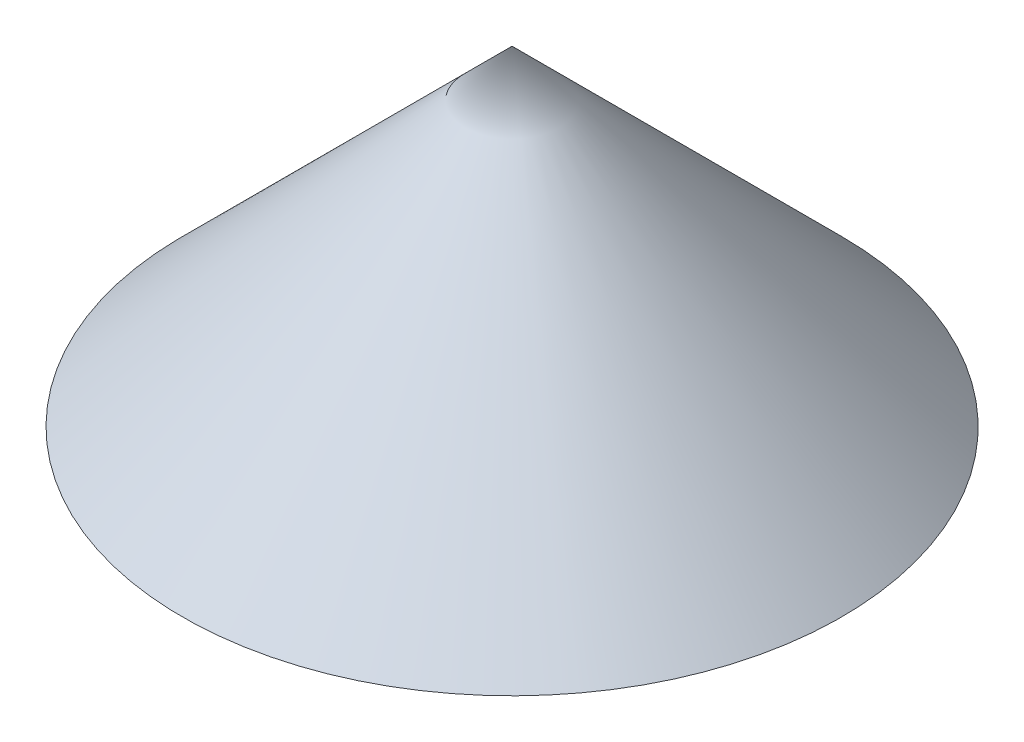
SolidWorks part; units mm, degrees
material "Air"
ref_plane "Front Plane" through (0, 0, 0) normal (0, 0, 1) x (1, 0, 0)
ref_plane "Top Plane" through (0, 0, 0) normal (0, 1, 0) x (1, 0, 0)
ref_plane "Right Plane" through (0, 0, 0) normal (1, 0, 0) x (0, 0, -1)
sketch "Sketch1" plane through (0, 0, 0) normal (0, 0, 1) x (1, 0, 0)
  line L0 (0, 0) -> (0, 10)
  line L1 (0, 10) -> (10, 0)
  line L2 (10, 0) -> (0, 0)
  dimension "D1" = 10
  dimension "D2" = 45
revolve "Revolve1" add sketch "Sketch1" angle 360 about L0
